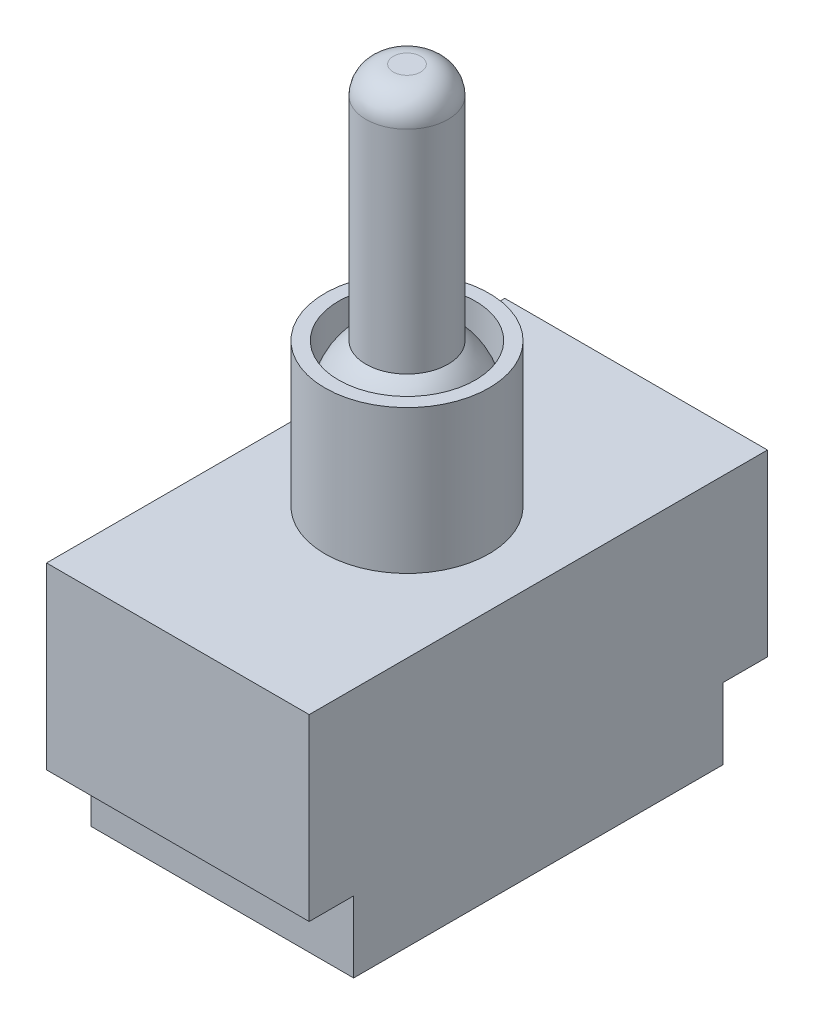
SolidWorks part; units mm, degrees
ref_plane "Спереди" through (0, 0, 0) normal (0, 0, 1) x (1, 0, 0)
ref_plane "Сверху" through (0, 0, 0) normal (0, 1, 0) x (1, 0, 0)
ref_plane "Справа" through (0, 0, 0) normal (1, 0, 0) x (0, 0, -1)
sketch "Sketch1" plane through (0, 0, 0) normal (0, 1, 0) x (1, 0, 0)
  line L1 (9.6, -16.75) -> (-9.6, -16.75)
  line L2 (9.6, -16.75) -> (9.6, 16.75)
  line L3 (9.6, 16.75) -> (-9.6, 16.75)
  line L4 (-9.6, -16.75) -> (-9.6, 16.75)
  line L5 (9.6, -16.75) -> (-9.6, 16.75) construction
  line L6 (9.6, 16.75) -> (-9.6, -16.75) construction
  point P0 (0, 0)
  dimension "D1" = 19.2
  dimension "D2" = 33.5
extrude "Boss-Extrude1" add sketch "Sketch1" along normal blind 13.1
sketch "Sketch2" plane through (0, 13.1, 0) normal (0, 1, 0) x (1, 0, 0)
  line L0 (-9.6, 16.75) -> (9.6, -16.75) construction
  circle A0 centre (0, 0) radius 6
  dimension "D1" = 12
extrude "Boss-Extrude2" add sketch "Sketch2" along normal blind 10.5
sketch "Sketch4" plane through (0, 23.6, 0) normal (0, 1, 0) x (1, 0, 0)
  circle A0 centre (0, 0) radius 5
  dimension "D1" = 10
extrude "Cut-Extrude1" cut sketch "Sketch4" against normal blind 4
sketch "Sketch5" plane through (0, 19.6, 0) normal (0, 1, 0) x (1, 0, 0)
  circle A0 centre (0, 0) radius 3
  dimension "D1" = 6
extrude "Boss-Extrude3" add sketch "Sketch5" along normal blind 21.5
sketch "Sketch3" plane through (0, 19.6, 0) normal (0, 1, 0) x (1, 0, 0)
  line L0 (0, -6) -> (0, 6) construction
  line L1 (0, -5) -> (0, 5)
  circle A0 centre (0, 0) radius 6 construction
  arc A1 (0, -5) -> (0, 5) centre (0, 0) cw
  point P7 (0, 0)
  dimension "D1" = 10
revolve "Revolve2" add sketch "Sketch3" angle 180 about L0
fillet "Fillet1" radius 2 1 edges at (0, 41.1, 3)
sketch "Sketch6" plane through (0, 0, 0) normal (0, -1, 0) x (1, 0, 0)
  line L0 (-9.6, -16.75) -> (-9.6, 16.75) construction
  line L1 (9.6, 13.5) -> (-9.6, 13.5)
  line L2 (9.6, 13.5) -> (9.6, -13.5)
  line L3 (9.6, -13.5) -> (-9.6, -13.5)
  line L4 (-9.6, 13.5) -> (-9.6, -13.5)
  line L5 (9.6, 13.5) -> (-9.6, -13.5) construction
  line L6 (9.6, -13.5) -> (-9.6, 13.5) construction
  point P0 (0, 0)
  dimension "D1" = 27
extrude "Boss-Extrude4" add sketch "Sketch6" along normal blind 5.2
